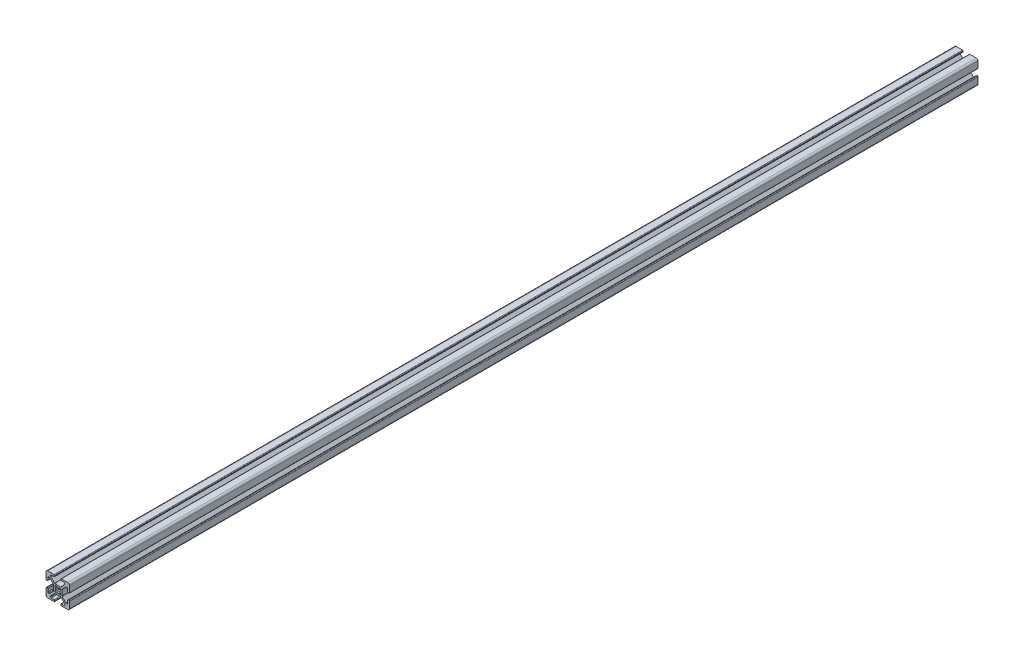
SolidWorks part; units mm, degrees
ref_plane "Front Plane" through (0, 0, 0) normal (0, 0, 1) x (1, 0, 0)
ref_plane "Top Plane" through (0, 0, 0) normal (0, 1, 0) x (1, 0, 0)
ref_plane "Right Plane" through (0, 0, 0) normal (1, 0, 0) x (0, 0, -1)
ref_plane "Plane1" through (0, 0, -25) normal (0, 0, -1) x (-1, 0, 0)
sketch "Sketch1" plane through (0, 0, -25) normal (0, 0, -1) x (-1, 0, 0)
  line L0 (2.3045, -2.1245) -> (2.1245, -2.3045)
  line L1 (-2.1245, -2.3045) -> (-2.3045, -2.1245)
  line L2 (-2.3045, 2.1245) -> (-2.1245, 2.3045)
  line L3 (2.1245, 2.3045) -> (2.3045, 2.1245)
  line L4 (10, -8.5) -> (10, -3.138)
  line L5 (9.492, -2.63) -> (9.008, -2.63)
  line L6 (8.5, -3.138) -> (8.5, -5.487)
  line L7 (7.992, -5.995) -> (7.2659, -5.995)
  line L8 (6.9067, -5.8462) -> (3.8038, -2.7433)
  line L9 (3.655, -2.3841) -> (3.655, 2.3838)
  line L10 (3.8038, 2.743) -> (6.907, 5.8462)
  line L11 (7.2662, 5.995) -> (7.992, 5.995)
  line L12 (8.5, 5.487) -> (8.5, 3.138)
  line L13 (9.008, 2.63) -> (9.492, 2.63)
  line L14 (10, 3.138) -> (10, 8.5)
  line L15 (8.5, 10) -> (3.138, 10)
  line L16 (2.63, 9.492) -> (2.63, 9.008)
  line L17 (3.138, 8.5) -> (5.487, 8.5)
  line L18 (5.995, 7.992) -> (5.995, 7.2659)
  line L19 (5.8462, 6.9067) -> (2.7433, 3.8038)
  line L20 (2.3841, 3.655) -> (-2.3838, 3.655)
  line L21 (-2.743, 3.8038) -> (-5.8462, 6.907)
  line L22 (-5.995, 7.2662) -> (-5.995, 7.992)
  line L23 (-5.487, 8.5) -> (-3.138, 8.5)
  line L24 (-2.63, 9.008) -> (-2.63, 9.492)
  line L25 (-3.138, 10) -> (-8.5, 10)
  line L26 (-10, 8.5) -> (-10, 3.138)
  line L27 (-9.492, 2.63) -> (-9.008, 2.63)
  line L28 (-8.5, 3.138) -> (-8.5, 5.487)
  line L29 (-7.992, 5.995) -> (-7.2659, 5.995)
  line L30 (-6.9067, 5.8462) -> (-3.8038, 2.7433)
  line L31 (-3.655, 2.3841) -> (-3.655, -2.3838)
  line L32 (-3.8038, -2.743) -> (-6.907, -5.8462)
  line L33 (-7.2662, -5.995) -> (-7.992, -5.995)
  line L34 (-8.5, -5.487) -> (-8.5, -3.138)
  line L35 (-9.008, -2.63) -> (-9.492, -2.63)
  line L36 (-10, -3.138) -> (-10, -8.5)
  line L37 (-8.5, -10) -> (-3.138, -10)
  line L38 (-2.63, -9.492) -> (-2.63, -9.008)
  line L39 (-3.138, -8.5) -> (-5.487, -8.5)
  line L40 (-5.995, -7.992) -> (-5.995, -7.2659)
  line L41 (-5.8462, -6.9067) -> (-2.7433, -3.8038)
  line L42 (-2.3841, -3.655) -> (2.3838, -3.655)
  line L43 (2.743, -3.8038) -> (5.8462, -6.907)
  line L44 (5.995, -7.2662) -> (5.995, -7.992)
  line L45 (5.487, -8.5) -> (3.138, -8.5)
  line L46 (2.63, -9.008) -> (2.63, -9.492)
  line L47 (3.138, -10) -> (8.5, -10)
  arc A0 (1.9358, 0.8037) -> (1.9358, -0.8037) centre (0, 0) cw
  arc A1 (1.9358, -0.8037) -> (2.3045, -2.1245) centre (1.748, -1.568) cw
  arc A2 (2.1245, -2.3045) -> (0.8037, -1.9358) centre (1.568, -1.748) cw
  arc A3 (0.8037, -1.9358) -> (-0.8037, -1.9358) centre (0, 0) cw
  arc A4 (-0.8037, -1.9358) -> (-2.1245, -2.3045) centre (-1.568, -1.748) cw
  arc A5 (-2.3045, -2.1245) -> (-1.9358, -0.8037) centre (-1.748, -1.568) cw
  arc A6 (-1.9358, -0.8037) -> (-1.9358, 0.8037) centre (0, 0) cw
  arc A7 (-1.9358, 0.8037) -> (-2.3045, 2.1245) centre (-1.748, 1.568) cw
  arc A8 (-2.1245, 2.3045) -> (-0.8037, 1.9358) centre (-1.568, 1.748) cw
  arc A9 (-0.8037, 1.9358) -> (0.8037, 1.9358) centre (0, 0) cw
  arc A10 (0.8037, 1.9358) -> (2.1245, 2.3045) centre (1.568, 1.748) cw
  arc A11 (2.3045, 2.1245) -> (1.9358, 0.8037) centre (1.748, 1.568) cw
  arc A12 (10, -3.138) -> (9.492, -2.63) centre (9.492, -3.138) ccw
  arc A13 (9.008, -2.63) -> (8.5, -3.138) centre (9.008, -3.138) ccw
  arc A14 (8.5, -5.487) -> (7.992, -5.995) centre (7.992, -5.487) cw
  arc A15 (7.2659, -5.995) -> (6.9067, -5.8462) centre (7.2659, -5.487) cw
  arc A16 (3.8038, -2.7433) -> (3.655, -2.3841) centre (4.163, -2.3841) cw
  arc A17 (3.655, 2.3838) -> (3.8038, 2.743) centre (4.163, 2.3838) cw
  arc A18 (6.907, 5.8462) -> (7.2662, 5.995) centre (7.2662, 5.487) cw
  arc A19 (7.992, 5.995) -> (8.5, 5.487) centre (7.992, 5.487) cw
  arc A20 (8.5, 3.138) -> (9.008, 2.63) centre (9.008, 3.138) ccw
  arc A21 (9.492, 2.63) -> (10, 3.138) centre (9.492, 3.138) ccw
  arc A22 (10, 8.5) -> (8.5, 10) centre (8.5, 8.5) ccw
  arc A23 (3.138, 10) -> (2.63, 9.492) centre (3.138, 9.492) ccw
  arc A24 (2.63, 9.008) -> (3.138, 8.5) centre (3.138, 9.008) ccw
  arc A25 (5.487, 8.5) -> (5.995, 7.992) centre (5.487, 7.992) cw
  arc A26 (5.995, 7.2659) -> (5.8462, 6.9067) centre (5.487, 7.2659) cw
  arc A27 (2.7433, 3.8038) -> (2.3841, 3.655) centre (2.3841, 4.163) cw
  arc A28 (-2.3838, 3.655) -> (-2.743, 3.8038) centre (-2.3838, 4.163) cw
  arc A29 (-5.8462, 6.907) -> (-5.995, 7.2662) centre (-5.487, 7.2662) cw
  arc A30 (-5.995, 7.992) -> (-5.487, 8.5) centre (-5.487, 7.992) cw
  arc A31 (-3.138, 8.5) -> (-2.63, 9.008) centre (-3.138, 9.008) ccw
  arc A32 (-2.63, 9.492) -> (-3.138, 10) centre (-3.138, 9.492) ccw
  arc A33 (-8.5, 10) -> (-10, 8.5) centre (-8.5, 8.5) ccw
  arc A34 (-10, 3.138) -> (-9.492, 2.63) centre (-9.492, 3.138) ccw
  arc A35 (-9.008, 2.63) -> (-8.5, 3.138) centre (-9.008, 3.138) ccw
  arc A36 (-8.5, 5.487) -> (-7.992, 5.995) centre (-7.992, 5.487) cw
  arc A37 (-7.2659, 5.995) -> (-6.9067, 5.8462) centre (-7.2659, 5.487) cw
  arc A38 (-3.8038, 2.7433) -> (-3.655, 2.3841) centre (-4.163, 2.3841) cw
  arc A39 (-3.655, -2.3838) -> (-3.8038, -2.743) centre (-4.163, -2.3838) cw
  arc A40 (-6.907, -5.8462) -> (-7.2662, -5.995) centre (-7.2662, -5.487) cw
  arc A41 (-7.992, -5.995) -> (-8.5, -5.487) centre (-7.992, -5.487) cw
  arc A42 (-8.5, -3.138) -> (-9.008, -2.63) centre (-9.008, -3.138) ccw
  arc A43 (-9.492, -2.63) -> (-10, -3.138) centre (-9.492, -3.138) ccw
  arc A44 (-10, -8.5) -> (-8.5, -10) centre (-8.5, -8.5) ccw
  arc A45 (-3.138, -10) -> (-2.63, -9.492) centre (-3.138, -9.492) ccw
  arc A46 (-2.63, -9.008) -> (-3.138, -8.5) centre (-3.138, -9.008) ccw
  arc A47 (-5.487, -8.5) -> (-5.995, -7.992) centre (-5.487, -7.992) cw
  arc A48 (-5.995, -7.2659) -> (-5.8462, -6.9067) centre (-5.487, -7.2659) cw
  arc A49 (-2.7433, -3.8038) -> (-2.3841, -3.655) centre (-2.3841, -4.163) cw
  arc A50 (2.3838, -3.655) -> (2.743, -3.8038) centre (2.3838, -4.163) cw
  arc A51 (5.8462, -6.907) -> (5.995, -7.2662) centre (5.487, -7.2662) cw
  arc A52 (5.995, -7.992) -> (5.487, -8.5) centre (5.487, -7.992) cw
  arc A53 (3.138, -8.5) -> (2.63, -9.008) centre (3.138, -9.008) ccw
  arc A54 (2.63, -9.492) -> (3.138, -10) centre (3.138, -9.492) ccw
  arc A55 (8.5, -10) -> (10, -8.5) centre (8.5, -8.5) ccw
extrude "Boss-Extrude1" add sketch "Sketch1" against normal blind 773.68
